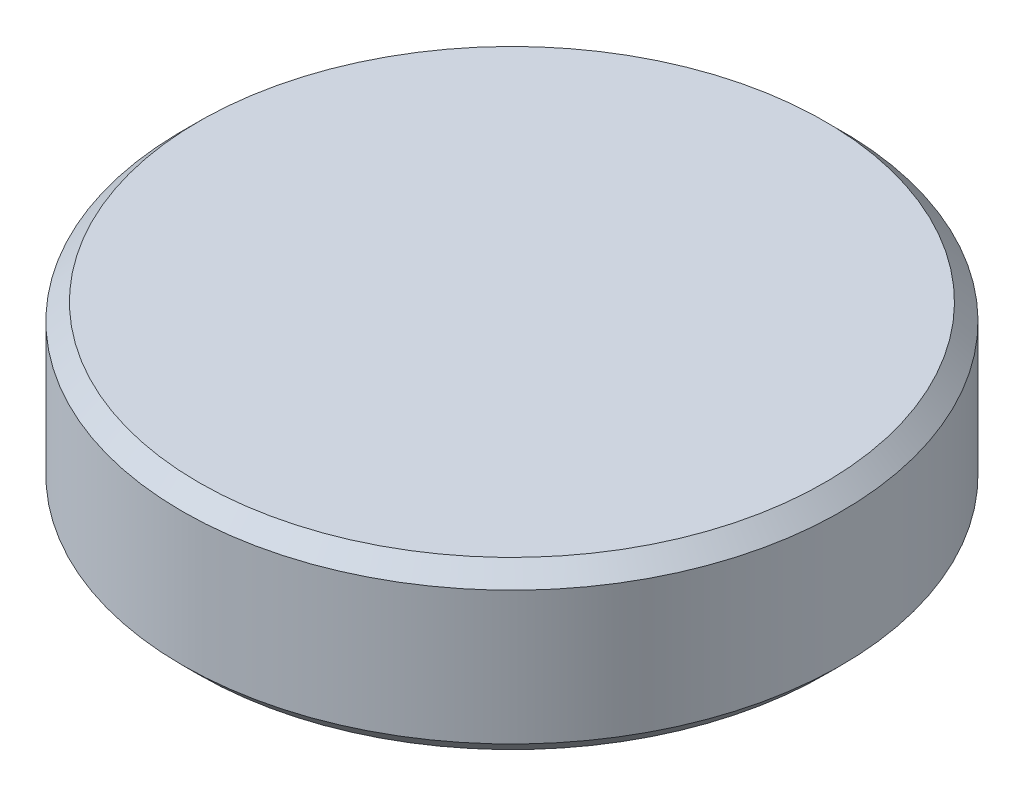
SolidWorks part; units mm, degrees
material "BUTYL"
ref_plane "Front" through (0, 0, 0) normal (0, 0, 1) x (1, 0, 0)
ref_plane "Top" through (0, 0, 0) normal (0, 1, 0) x (1, 0, 0)
ref_plane "Right" through (0, 0, 0) normal (1, 0, 0) x (0, 0, -1)
sketch "Sketch1" plane through (0, 0, 0) normal (0, 1, 0) x (1, 0, 0)
  circle A0 centre (0, 0) radius 4.95
  dimension "D1" = 9.9
extrude "Boss-Extrude1" add sketch "Sketch1" along normal blind 2.5
chamfer "Chamfer1" distance 0.25 angle 45 2 edges at (0, 0, 4.95) (0, 2.5, 4.95)
